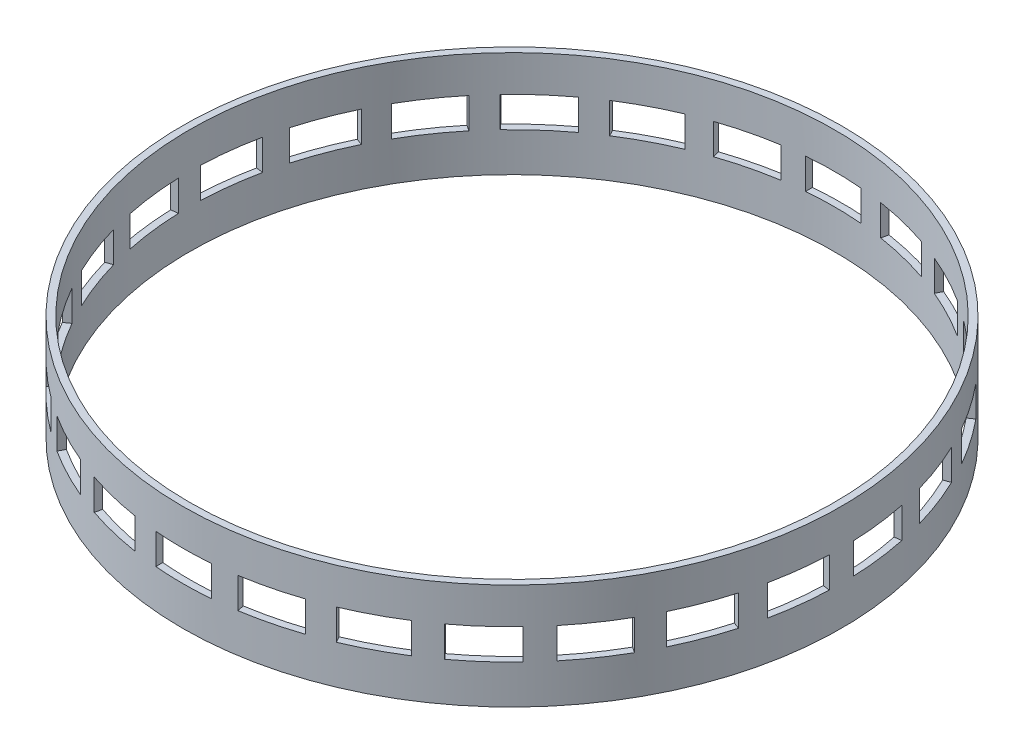
SolidWorks part; units mm, degrees
material "ABS PC"
ref_plane "Front" through (0, 0, 0) normal (0, 0, 1) x (1, 0, 0)
ref_plane "Top" through (0, 0, 0) normal (0, 1, 0) x (1, 0, 0)
ref_plane "Right" through (0, 0, 0) normal (1, 0, 0) x (0, 0, -1)
sketch "Sketch1" plane through (0, 0, 0) normal (0, 1, 0) x (1, 0, 0)
  circle A0 centre (0, 0) radius 116
  circle A1 centre (0, 0) radius 118.5
  dimension "D1" = 237
  dimension "D2" = 232
extrude "Boss-Extrude1" add sketch "Sketch1" along normal blind 38
sketch "Sketch2" plane through (0, 0, 0) normal (0, 0, 1) x (1, 0, 0)
  line L1 (-10, 25) -> (10, 25)
  line L2 (-10, 25) -> (-10, 14)
  line L3 (-10, 14) -> (10, 14)
  line L4 (10, 25) -> (10, 14)
  line L5 (-118.5, 0) -> (118.5, 0) construction
  line L6 (-116, 0) -> (116, 0) construction
  line L7 (0, 0) -> (0, 25) construction
  dimension "D1" = 14
  dimension "D2" = 11
  dimension "D3" = 20
extrude "Cut-Extrude1" cut sketch "Sketch2" against normal through all both and the other way through all
pattern_circular "CirPattern1" count 13 over 360 about axis through (0, 0, 0) along (0, 1, 0) of "Cut-Extrude1"
